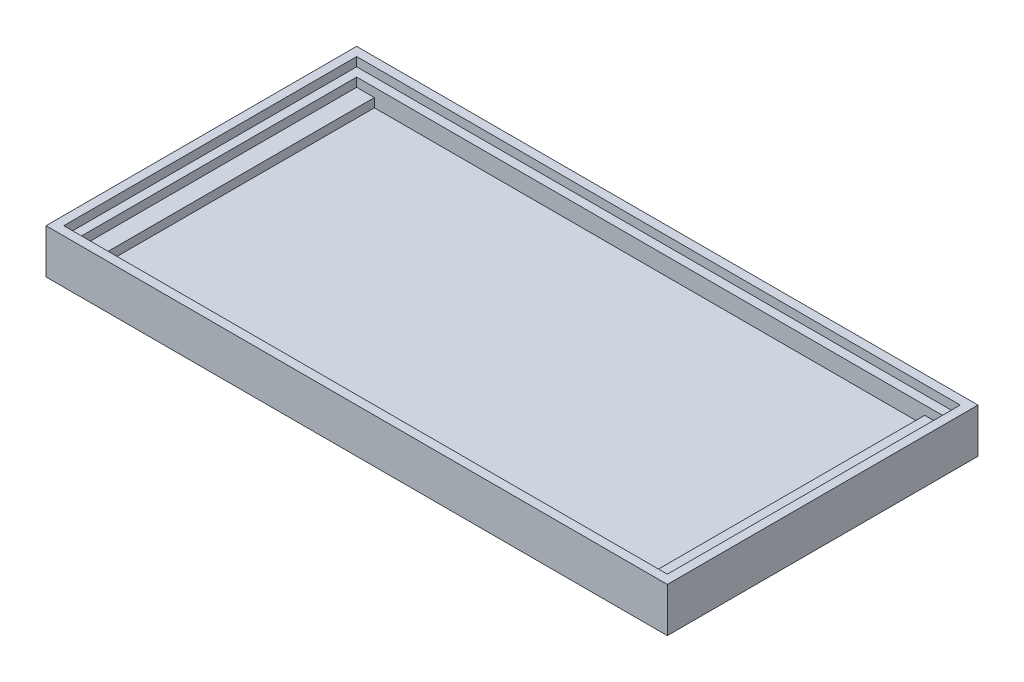
SolidWorks part; units mm, degrees
ref_plane "Front Plane" through (0, 0, 0) normal (0, 0, 1) x (1, 0, 0)
ref_plane "Top Plane" through (0, 0, 0) normal (0, 1, 0) x (1, 0, 0)
ref_plane "Right Plane" through (0, 0, 0) normal (1, 0, 0) x (0, 0, -1)
sketch "Sketch1" plane through (0, 0, 0) normal (0, 1, 0) x (1, 0, 0)
  line L4 (68, 33) -> (-2, 33)
  line L5 (-2, 33) -> (-2, -2)
  line L6 (-2, -2) -> (68, -2)
  line L7 (68, -2) -> (68, 33)
  dimension "D1" = 70
  dimension "D2" = 35
  dimension "D3" = 70
  dimension "D4" = 35
extrude "Boss-Extrude1" add sketch "Sketch1" along normal blind 2
sketch "Sketch2" plane through (0, 2, 0) normal (0, 1, 0) x (1, 0, 0)
  line L0 (66, 31) -> (0, 31)
  line L1 (0, 31) -> (0, 0)
  line L2 (0, 0) -> (66, 0)
  line L3 (66, 0) -> (66, 31)
  line L4 (68, -2) -> (68, 33)
  line L5 (68, 33) -> (-2, 33)
  line L6 (-2, 33) -> (-2, -2)
  line L7 (-2, -2) -> (68, -2)
  line L8 (68, -2) -> (68, 33)
  line L9 (68, 33) -> (-2, 33)
  line L10 (-2, 33) -> (-2, -2)
  line L11 (-2, -2) -> (68, -2)
  dimension "D1" = 0
  dimension "D2" = 2
extrude "Boss-Extrude2" add sketch "Sketch2" along normal blind 2
sketch "Sketch3" plane through (0, 2, 0) normal (0, 1, 0) x (1, 0, 0)
  line L0 (0, 31) -> (2, 31)
  line L1 (66, 31) -> (0, 31) construction
  line L2 (2, 31) -> (2, 0)
  line L3 (0, 0) -> (66, 0) construction
  line L4 (2, 0) -> (0, 0)
  line L5 (0, 0) -> (0, 31)
  line L6 (66, 31) -> (64, 31)
  line L7 (66, 31) -> (0, 31) construction
  line L8 (64, 31) -> (64, 0)
  line L9 (0, 0) -> (66, 0) construction
  line L10 (64, 0) -> (66, 0)
  line L11 (66, 0) -> (66, 31)
  dimension "D1" = 2
  dimension "D2" = 2
extrude "Boss-Extrude3" add sketch "Sketch3" along normal blind 1
sketch "Sketch4" plane through (0, 4, 0) normal (0, 1, 0) x (1, 0, 0)
  line L0 (68, 33) -> (-2, 33) construction
  line L1 (-2, 33) -> (-2, -2) construction
  line L2 (-2, -2) -> (68, -2) construction
  line L3 (68, -2) -> (68, 33) construction
  line L4 (68, 33) -> (-2, 33)
  line L5 (-2, 33) -> (-2, -2)
  line L6 (-2, -2) -> (68, -2)
  line L7 (68, -2) -> (68, 33)
  line L8 (67, 32) -> (-1, 32)
  line L9 (-1, 32) -> (-1, -1)
  line L10 (-1, -1) -> (67, -1)
  line L11 (67, -1) -> (67, 32)
  dimension "D1" = 1
extrude "Boss-Extrude4" add sketch "Sketch4" along normal blind 1
